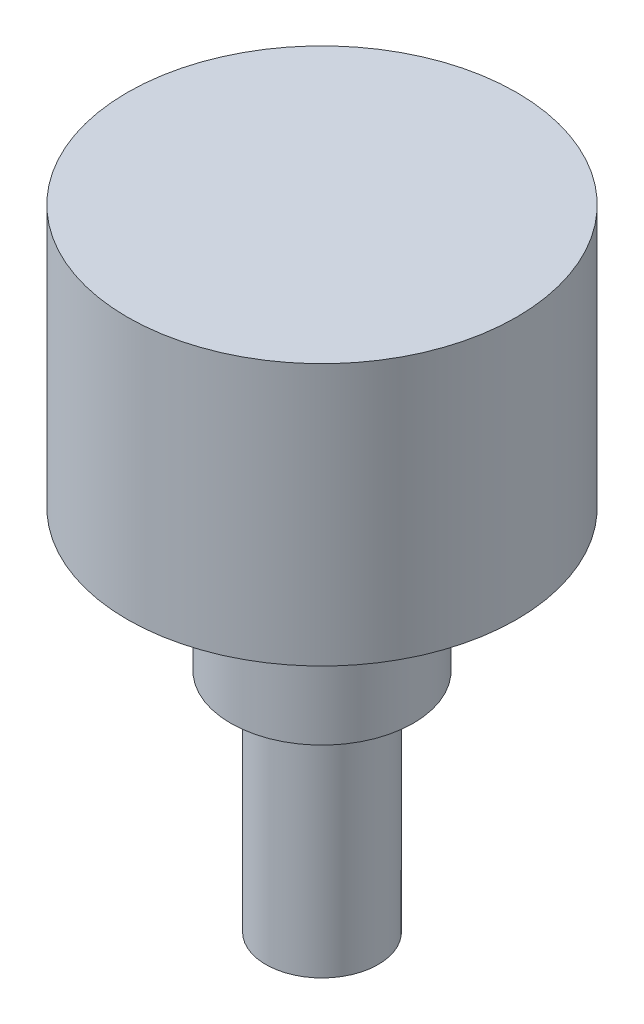
SolidWorks part; units mm, degrees
ref_plane "Front Plane" through (0, 0, 0) normal (0, 0, 1) x (1, 0, 0)
ref_plane "Top Plane" through (0, 0, 0) normal (0, 1, 0) x (1, 0, 0)
ref_plane "Right Plane" through (0, 0, 0) normal (1, 0, 0) x (0, 0, -1)
sketch "Sketch1" plane through (0, 0, 0) normal (0, 1, 0) x (1, 0, 0)
  circle A0 centre (0, 0) radius 11
  dimension "D1" = 22
extrude "Boss-Extrude1" add sketch "Sketch1" along normal blind 14.8
sketch "Sketch2" plane through (0, 0, 0) normal (0, -1, 0) x (1, 0, 0)
  circle A0 centre (0, 0) radius 5.16
  dimension "D1" = 10.32
extrude "Boss-Extrude2" add sketch "Sketch2" along normal blind 8
sketch "Sketch3" plane through (0, -8, 0) normal (0, -1, 0) x (-1, 0, 0)
  circle A0 centre (0, 0) radius 3.175
  dimension "D1" = 6.35
extrude "Boss-Extrude3" add sketch "Sketch3" along normal blind 12.8
sketch "Sketch4" plane through (0, 0, 0) normal (0, -1, 0) x (1, 0, 0)
  line L0 (0, 0) -> (7.9, 0) construction
  circle A0 centre (7.9, 0) radius 0.75
  dimension "D2" = 1.5
  dimension "D1" = 7.9
extrude "Boss-Extrude4" add sketch "Sketch4" along normal blind 2.1
